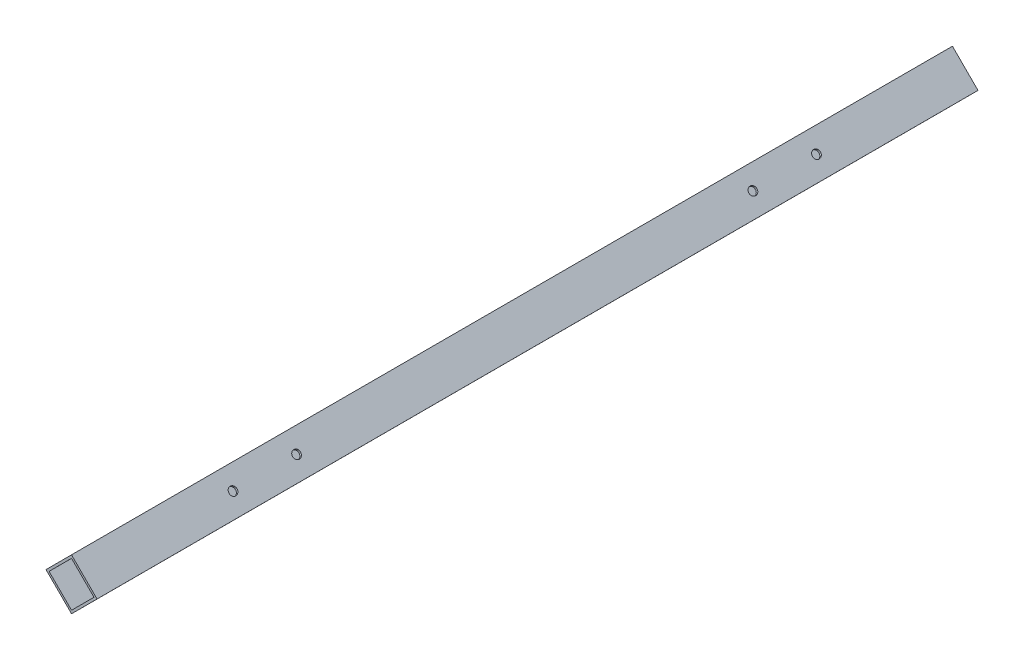
SolidWorks part; units mm, degrees
material "可鍛鑄鐵"
ref_plane "前基準面" through (0, 0, 0) normal (0, 0, 1) x (1, 0, 0)
ref_plane "上基準面" through (0, 0, 0) normal (0, 1, 0) x (1, 0, 0)
ref_plane "右基準面" through (0, 0, 0) normal (1, 0, 0) x (0, 0, -1)
sketch "草圖1" plane through (0, 0, 0) normal (0, 0, 1) x (1, 0, 0)
  line L0 (0, 0) -> (17.6938, -17.6615)
  line L1 (0, 0) -> (-17.6615, -17.6938)
  line L2 (17.6938, -17.6615) -> (0.0323, -35.3553)
  line L3 (-17.6615, -17.6938) -> (0.0323, -35.3553)
  line L4 (0.0019, -2.1213) -> (-15.5402, -17.6919)
  line L5 (0.0019, -2.1213) -> (15.5725, -17.6635)
  line L6 (-15.5402, -17.6919) -> (0.0303, -33.234)
  line L7 (15.5725, -17.6635) -> (0.0303, -33.234)
  point P0 (8.8469, -8.8308)
  dimension "D1" = 25
  dimension "D2" = 25
  dimension "D3" = 1.5
  dimension "D4" = 1.5
  dimension "D5" = 1.5
  dimension "D6" = 1.5
extrude "填料-伸長1" add sketch "草圖1" along normal blind 610
sketch "草圖2" plane through (0, 0, 0) normal (0.7065, 0.7078, 0) x (0.7078, -0.7065, 0)
  line L0 (25, -610) -> (0, -610) construction
  line L1 (25, -610) -> (25, 0) construction
  line L2 (25, 0) -> (0, 0) construction
  line L3 (0, -610) -> (0, 0) construction
  circle A0 centre (12.5, -463) radius 2.75
  circle A1 centre (12.5, -507) radius 2.75
  circle A2 centre (12.5, -103) radius 2.75
  circle A3 centre (12.5, -147) radius 2.75
  dimension "D1" = 5.5
  dimension "D2" = 5.5
  dimension "D4" = 103
  dimension "D5" = 12.5
  dimension "D6" = 12.5
  dimension "D7" = 5.5
  dimension "D8" = 5.5
  dimension "D9" = 44
  dimension "D10" = 103
  dimension "D11" = 12.5
  dimension "D3" = 44
extrude "除料-伸長1" cut sketch "草圖2" against normal through all
